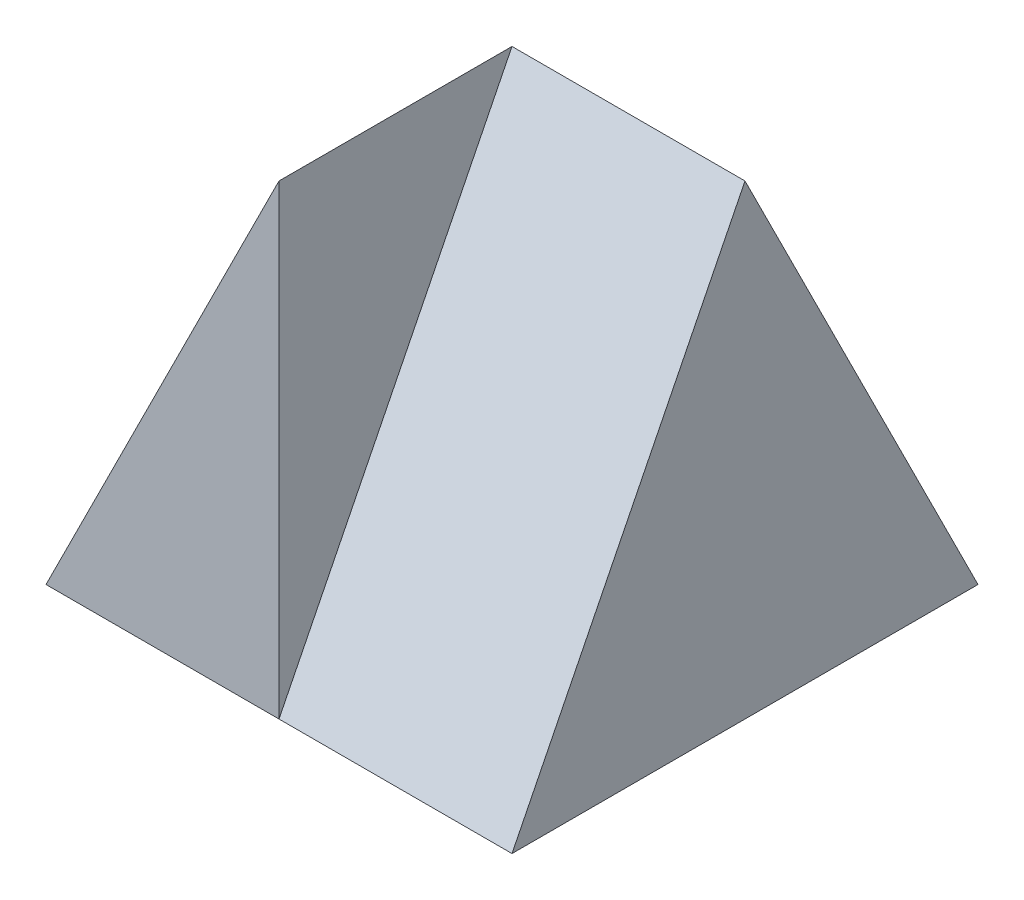
SolidWorks part; units mm, degrees
ref_plane "Front Plane" through (0, 0, 0) normal (0, 0, 1) x (1, 0, 0)
ref_plane "Top Plane" through (0, 0, 0) normal (0, 1, 0) x (1, 0, 0)
ref_plane "Right Plane" through (0, 0, 0) normal (1, 0, 0) x (0, 0, -1)
sketch "Sketch1" plane through (0, 0, 0) normal (0, 0, 1) x (1, 0, 0)
  line L1 (0, 0) -> (40, 0)
  line L2 (0, 0) -> (0, 40)
  line L3 (0, 40) -> (40, 40)
  line L4 (40, 0) -> (40, 40)
  dimension "D1" = 40
  dimension "D2" = 40
extrude "Boss-Extrude1" add sketch "Sketch1" along normal blind 40
sketch "Sketch2" plane through (0, 0, 40) normal (0, 0, 1) x (1, 0, 0)
  line L0 (0, 0) -> (20, 40)
  line L1 (40, 40) -> (0, 40) construction
  line L2 (20, 40) -> (0, 40)
  line L3 (0, 40) -> (0, 0)
extrude "Cut-Extrude1" cut sketch "Sketch2" against normal blind 40
sketch "Sketch3" plane through (0, 0, 0) normal (0, -1, 0) x (1, 0, 0)
  line L0 (0, 20) -> (20, 0)
  line L1 (0, 40) -> (0, 0) construction
  line L2 (0, 0) -> (40, 0) construction
  line L3 (20, 0) -> (0, 0)
  line L4 (0, 0) -> (0, 20)
extrude "Cut-Extrude2" cut sketch "Sketch3" against normal blind 40
sketch "Sketch5" plane through (40, 0, 0) normal (1, 0, 0) x (0, 0, -1)
  line L0 (-40, 0) -> (-20, 40)
  line L1 (-40, 40) -> (0, 40) construction
  line L2 (-20, 40) -> (0, 0)
  line L3 (0, 0) -> (0, 40)
  line L4 (0, 40) -> (-40, 40)
  line L5 (-40, 40) -> (-40, 0)
  line L6 (-40, 0) -> (-40.6428, -1.1037)
  line M1 (0, 0) -> (0, 40)
  line M2 (0, 40) -> (-40, 40)
  line M3 (-40, 40) -> (-40, 0)
extrude "Cut-Extrude5" cut sketch "Sketch5" against normal blind 20 contours L0 M3 M2 | L2 M2 M1
ref_plane "Plane1" through (8.8889, -4.4444, 8.8889) normal (-0.6667, 0.3333, -0.6667) x (-0.7454, -0.2981, 0.5963)
sketch "Sketch6" plane through (8.8889, -4.4444, 8.8889) normal (-0.6667, 0.3333, -0.6667) x (-0.7454, -0.2981, 0.5963)
  line L0 (11.9257, 8.9443) -> (-14.9071, 0)
  line L1 (-14.9071, 0) -> (-14.9071, 44.7214)
  line L2 (-14.9071, 44.7214) -> (11.9257, 8.9443)
extrude "Cut-Extrude6" cut sketch "Sketch6" along normal blind 20
sketch "Sketch7" plane through (11.1111, 4.4444, -8.8889) normal (-0.7454, -0.2981, 0.5963) x (0.5536, 0.2215, 0.8028)
  line L0 (11.0727, -7.4278) -> (35.9864, 29.7113)
  line L1 (35.9864, 29.7113) -> (18.7385, 20.5693)
  line L2 (18.7385, 20.5693) -> (11.0727, -7.4278)
extrude "Cut-Extrude7" cut sketch "Sketch7" against normal blind 20
sketch "Sketch8" plane through (-5.521, 6.7357, -3.5335) normal (0.5874, -0.7167, 0.376) x (0.8093, 0.5202, -0.2729)
  line L0 (31.5355, 36.2929) -> (23.9314, 18.314)
  line L1 (23.9314, 18.314) -> (31.5355, 15.0979)
  line L2 (31.5355, 15.0979) -> (31.5355, 36.2929)
extrude "Cut-Extrude8" cut sketch "Sketch8" against normal blind 20
sketch "Sketch9" plane through (20, 0, 0) normal (1, 0, 0) x (0, 0, -1)
  line L0 (-20, 40) -> (0, 40)
  line L1 (0, 40) -> (0, 0)
  line L2 (0, 0) -> (-1.2308, 30.1538)
  line L3 (-1.2308, 30.1538) -> (-20, 40)
extrude "Cut-Extrude9" cut sketch "Sketch9" against normal blind 20
sketch "Sketch10" plane through (7.99, -0.3995, 9.7878) normal (0.6321, -0.0316, 0.7743) x (0.7749, 0.0258, -0.6315)
  line L0 (15.4984, 30.179) -> (7.5571, 27.9202)
  line L1 (7.5571, 27.9202) -> (15.4984, 0)
  line L2 (15.4984, 0) -> (15.4984, 30.179)
extrude "Cut-Extrude10" cut sketch "Sketch10" against normal blind 20
sketch "Sketch11" plane through (8.2561, 16.5122, 18.5762) normal (0.3152, 0.6305, 0.7093) x (0.949, -0.2094, -0.2356)
  line L0 (10.5139, 21.5738) -> (12.3749, 21.7196)
  line L1 (12.3749, 21.7196) -> (5.8904, 16.6091)
  line L2 (5.8904, 16.6091) -> (10.5139, 21.5738)
extrude "Cut-Extrude11" cut sketch "Sketch11" against normal blind 20
sketch "Sketch12" plane through (10, 0, 10) normal (-0.7071, 0, -0.7071) x (-0.7071, 0, 0.7071)
  line L0 (-12.4087, 30.0303) -> (-12.4016, 30.1538)
  line L1 (-12.4016, 30.1538) -> (-11.6445, 30.4347)
  line L2 (-11.6445, 30.4347) -> (-12.4087, 30.0303)
extrude "Cut-Extrude12" cut sketch "Sketch12" against normal blind 20
sketch "Sketch15" plane through (0, 23.1401, -12.1391) normal (0, 0.8855, -0.4645) x (1, 0, 0)
  line L0 (18.2339, -15.7023) -> (20, -15.0979)
  line L1 (20, -15.0979) -> (18.7692, -15.0979)
  line L2 (18.2339, -15.7023) -> (18.7692, -15.0979)
extrude "Cut-Extrude17" cut sketch "Sketch15" against normal blind 20
sketch "Sketch16" plane through (0, 0, 0) normal (0, 0.0408, -0.9992) x (-1, 0, 0)
  line L0 (-18.7743, 30.0553) -> (-18.7692, 30.179)
  line L1 (-18.7692, 30.179) -> (-20, 30.179)
  line L2 (-20, 30.179) -> (-18.7743, 30.0553)
extrude "Cut-Extrude18" cut sketch "Sketch16" against normal blind 7
sketch "Sketch20" plane through (0, 0, 0) normal (0, 0.4472, -0.8944) x (-1, 0, 0)
  line L1 (-40, 44.7214) -> (-20, 44.7214)
  line L2 (-40, 44.7214) -> (-40, 0)
  line L3 (-40, 0) -> (-20, 0)
  line L4 (-20, 44.7214) -> (-20, 0)
extrude "Boss-Extrude6" add sketch "Sketch20" against normal blind 7
sketch "Sketch21" plane through (40, 0, 0) normal (1, 0, 0) x (0, 0, -1)
  line L0 (-7.8262, 0) -> (0, 0)
  line L1 (0, 0) -> (-6.261, -3.1305)
  line L2 (-6.261, -3.1305) -> (-7.8262, 0)
  line L3 (-23.9131, 32.1738) -> (-20, 40)
  line L4 (-20, 40) -> (-26.261, 36.8695)
  line L5 (-26.261, 36.8695) -> (-23.9131, 32.1738)
extrude "Cut-Extrude20" cut sketch "Sketch21" against normal blind 20
sketch "Sketch22" plane through (8.8889, -4.4444, 8.8889) normal (-0.6667, 0.3333, -0.6667) x (-0.5963, 0.2981, 0.7454)
  line L0 (14.9071, 44.7214) -> (-11.9257, 8.9443)
  line L1 (-11.9257, 8.9443) -> (14.9071, 0)
  line L2 (14.9071, 0) -> (14.9071, 44.7214)
extrude "Boss-Extrude7" add sketch "Sketch22" against normal blind 2
sketch "Sketch23" plane through (0, 16, 32) normal (0, 0.4472, 0.8944) x (1, 0, 0)
  line L1 (40, -17.8885) -> (20, -17.8885)
  line L2 (40, -17.8885) -> (40, 26.8328)
  line L3 (40, 26.8328) -> (20, 26.8328)
  line L4 (20, -17.8885) -> (20, 26.8328)
extrude "Cut-Extrude21" cut sketch "Sketch23" along normal blind 2
sketch "Sketch24" plane through (0, 0, 0) normal (0, -1, 0) x (1, 0, 0)
  line L1 (40, 0) -> (0, 0)
  line L2 (40, 0) -> (40, 40)
  line L3 (40, 40) -> (0, 40)
  line L4 (0, 0) -> (0, 40)
extrude "Cut-Extrude22" cut sketch "Sketch24" along normal blind 20
sketch "Sketch25" plane through (8.8889, -4.4444, 8.8889) normal (-0.6667, 0.3333, -0.6667) x (-0.5963, 0.2981, 0.7454)
  line L0 (14.9071, 44.7214) -> (14.9071, 0)
  line L1 (14.9071, 0) -> (-11.9257, 8.9443)
  line L2 (-11.9257, 8.9443) -> (14.9071, 44.7214)
  line L3 (14.9071, 44.7214) -> (14.9855, 44.4465)
  line M1 (14.9071, 44.7214) -> (-11.9257, 8.9443)
  line M2 (-11.9257, 8.9443) -> (14.9071, 0)
  line M3 (14.9071, 0) -> (14.9071, 44.7214)
extrude "Boss-Extrude8" add sketch "Sketch25" against normal blind 5 contours M3 M1 M2
sketch "Sketch26" plane through (0, 16, 32) normal (0, 0.4472, 0.8944) x (1, 0, 0)
  line L1 (40, -17.8885) -> (20, -17.8885)
  line L2 (40, -17.8885) -> (40, 26.8328)
  line L3 (40, 26.8328) -> (20, 26.8328)
  line L4 (20, -17.8885) -> (20, 26.8328)
extrude "Cut-Extrude23" cut sketch "Sketch26" along normal blind 5
sketch "Sketch27" plane through (0, 0, 0) normal (0, -1, 0) x (1, 0, 0)
  line L1 (40, 40) -> (0, 40)
  line L2 (40, 40) -> (40, 0)
  line L3 (40, 0) -> (0, 0)
  line L4 (0, 40) -> (0, 0)
extrude "Cut-Extrude24" cut sketch "Sketch27" along normal blind 5
